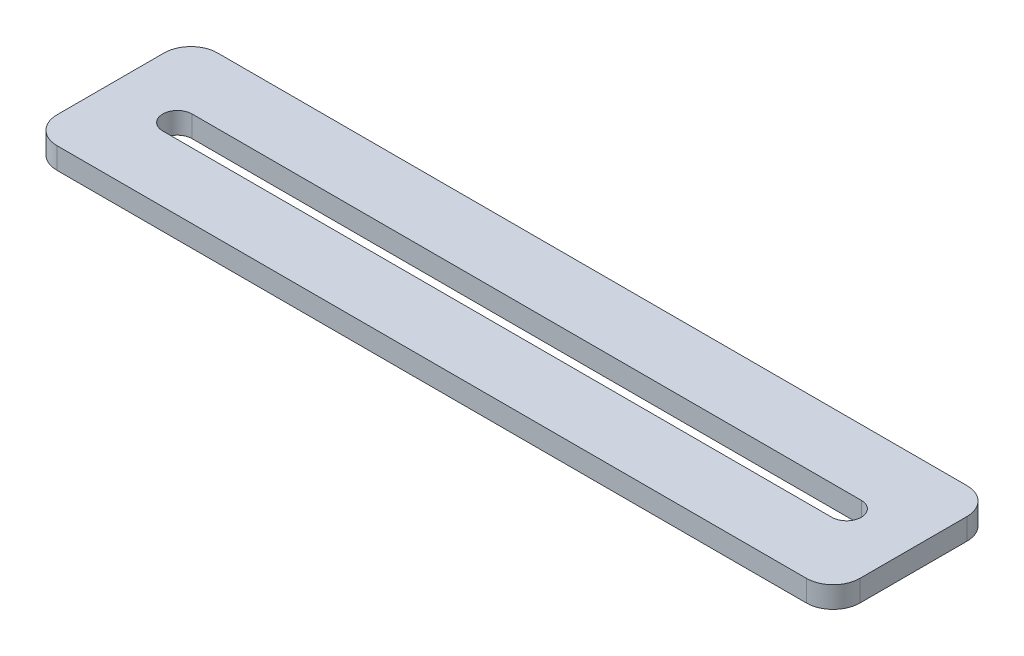
SolidWorks part; units mm, degrees
ref_plane "Front Plane" through (0, 0, 0) normal (0, 0, 1) x (1, 0, 0)
ref_plane "Top Plane" through (0, 0, 0) normal (0, 1, 0) x (1, 0, 0)
ref_plane "Right Plane" through (0, 0, 0) normal (1, 0, 0) x (0, 0, -1)
sketch "Sketch1" plane through (0, 0, 0) normal (0, 1, 0) x (1, 0, 0)
  line L0 (-62.5, 0) -> (62.5, 0) construction
  line L1 (-75, -15) -> (75, -15)
  line L2 (-75, -15) -> (-75, 15)
  line L3 (-75, 15) -> (75, 15)
  line L4 (75, -15) -> (75, 15)
  line L5 (-75, -15) -> (75, 15) construction
  line L6 (-75, 15) -> (75, -15) construction
  line L7 (-62.5, 2.75) -> (62.5, 2.75)
  line L8 (-62.5, -2.75) -> (62.5, -2.75)
  arc A0 (-62.5, 2.75) -> (-62.5, -2.75) centre (-62.5, 0) ccw
  arc A1 (62.5, -2.75) -> (62.5, 2.75) centre (62.5, 0) ccw
  point P0 (0, 0)
  point P8 (0, 0)
  dimension "D1" = 150
  dimension "D2" = 30
  dimension "D3" = 125
  dimension "D4" = 5.5
extrude "Boss-Extrude1" add sketch "Sketch1" along normal blind 4
fillet "Fillet1" radius 5 4 edges at (75, 2, 15) (75, 2, -15) (-75, 2, -15) (-75, 2, 15)
